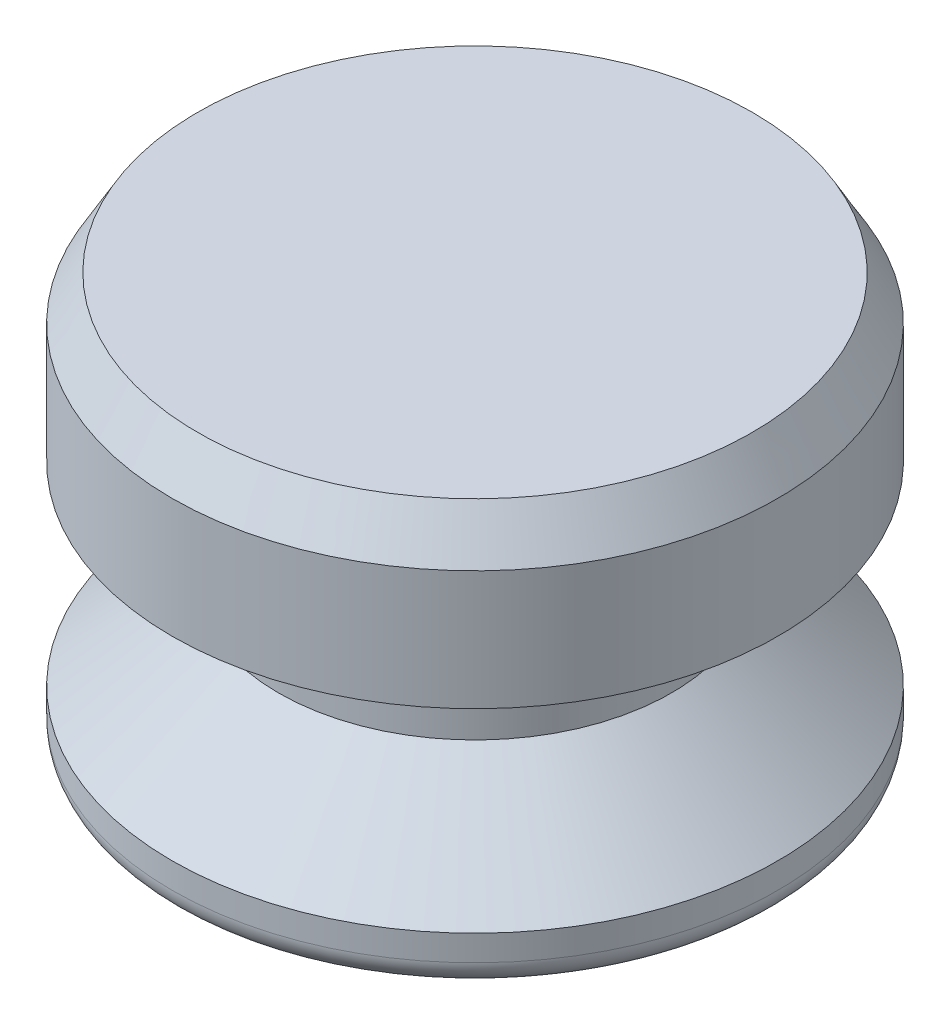
SolidWorks part; units mm, degrees
ref_plane "Front Plane" through (0, 0, 0) normal (0, 0, 1) x (1, 0, 0)
ref_plane "Top Plane" through (0, 0, 0) normal (0, 1, 0) x (1, 0, 0)
ref_plane "Right Plane" through (0, 0, 0) normal (1, 0, 0) x (0, 0, -1)
sketch "Sketch1" plane through (0, 0, 0) normal (0, 0, 1) x (1, 0, 0)
  line L0 (0, 0) -> (0, 12.7) construction
  line L1 (0, 0) -> (-9.398, 0)
  line L2 (-9.398, 0) -> (-9.398, 1.5875)
  line L4 (-6.096, 4.445) -> (-6.096, 7.62)
  line L5 (-6.096, 7.62) -> (-9.398, 7.62)
  line L6 (-9.398, 7.62) -> (-9.398, 12.7)
  line L7 (-9.398, 12.7) -> (0, 12.7)
  line L8 (-9.525, 16.6801) -> (-9.525, -9.6051) construction
  line L9 (0, 0) -> (0, 12.7)
  line L10 (-6.096, 4.445) -> (-9.398, 1.5875)
  dimension "D1" = 12.7
  dimension "D2" = 9.398
  dimension "D3" = 3.175
  dimension "D4" = 1.5875
  dimension "D5" = 9.525
  dimension "D6" = 6.096
  dimension "D7" = 7.62
revolve "Revolve1" add sketch "Sketch1" angle 360 about L9
fillet "Fillet1" radius 0.7937 1 edges at (0, 0, -9.398)
chamfer "Chamfer1" distance 0.7937 angle 60 1 edges at (0, 12.7, -9.398)
